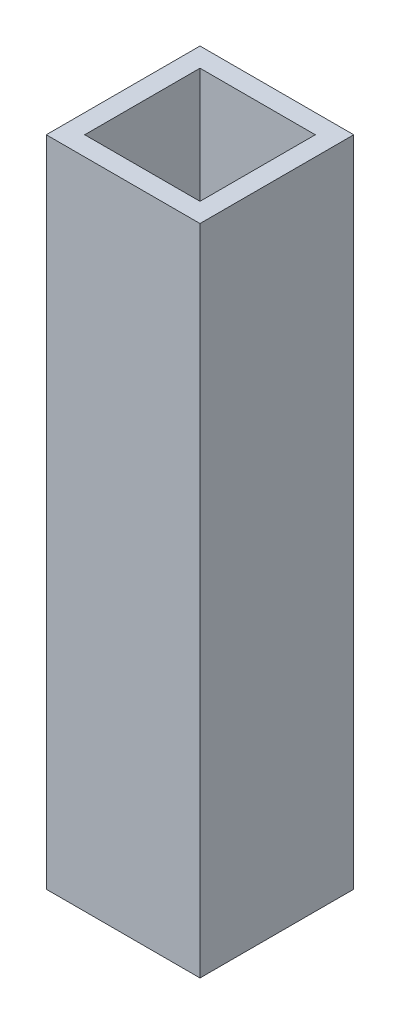
SolidWorks part; units mm, degrees
material "1060 Alloy"
ref_plane "Front Plane" through (0, 0, 0) normal (0, 0, 1) x (1, 0, 0)
ref_plane "Top Plane" through (0, 0, 0) normal (0, 1, 0) x (1, 0, 0)
ref_plane "Right Plane" through (0, 0, 0) normal (1, 0, 0) x (0, 0, -1)
sketch "Sketch1" plane through (0, 0, 0) normal (0, 1, 0) x (1, 0, 0)
  line L0 (-9.525, -9.525) -> (-9.525, 9.525)
  line L1 (-12.7, -12.7) -> (12.7, -12.7)
  line L2 (-12.7, -12.7) -> (-12.7, 12.7)
  line L3 (-12.7, 12.7) -> (12.7, 12.7)
  line L4 (12.7, -12.7) -> (12.7, 12.7)
  line L5 (-12.7, -12.7) -> (12.7, 12.7) construction
  line L6 (-12.7, 12.7) -> (12.7, -12.7) construction
  line L7 (-9.525, 9.525) -> (9.525, 9.525)
  line L8 (9.525, -9.525) -> (9.525, 9.525)
  line L9 (-9.525, -9.525) -> (9.525, -9.525)
  point P0 (0, 0)
  dimension "D1" = 25.4
  dimension "D2" = 25.4
  dimension "D3" = 3.175
extrude "Boss-Extrude1" add sketch "Sketch1" along normal blind 107.95 contours L1 L4 L3 L2 L9 L0 L7 L8
